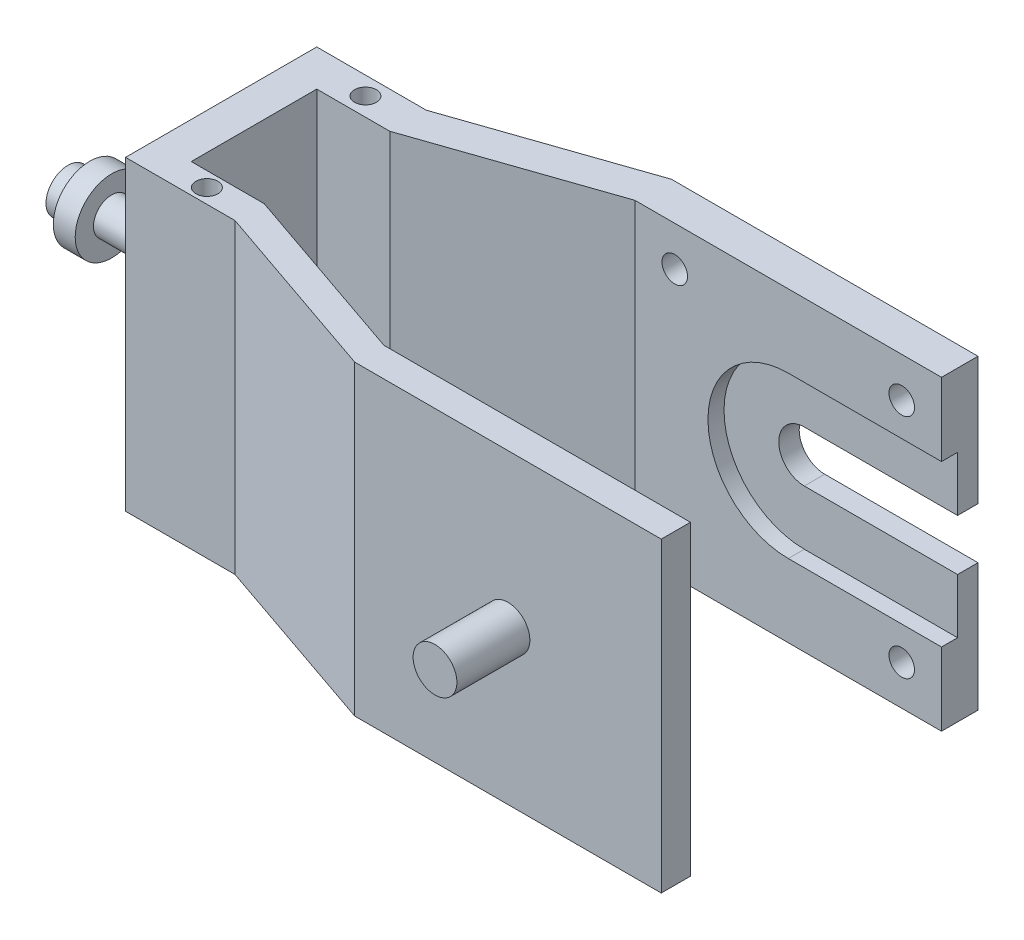
SolidWorks part; units mm, degrees
ref_plane "Front Plane" through (0, 0, 0) normal (0, 0, 1) x (1, 0, 0)
ref_plane "Top Plane" through (0, 0, 0) normal (0, 1, 0) x (1, 0, 0)
ref_plane "Right Plane" through (0, 0, 0) normal (1, 0, 0) x (0, 0, -1)
sketch "Sketch1" plane through (0, 0, 0) normal (0, 1, 0) x (1, 0, 0)
  line L0 (0, 0) -> (0, 17.2)
  line L1 (0, 0) -> (0, -17.2)
  line L2 (0, 17.2) -> (-42, 17.2)
  line L3 (0, -17.2) -> (-42, -17.2)
  line L4 (0, 0) -> (-77, 0)
  line L5 (0, 8.6) -> (-67, 8.6)
  line L6 (0, -8.6) -> (-67, -8.6)
  line L7 (-42, 17.2) -> (-67, 8.6)
  line L8 (-77, 8.6) -> (-67, 8.6)
  line L9 (-77, 8.6) -> (-77, -8.6)
  line L10 (-77, -8.6) -> (-67, -8.6)
  line L11 (-67, -8.6) -> (-42, -17.2)
  line L12 (0, 17.2) -> (0, 22.2)
  line L13 (0, 22.2) -> (-42, 22.2)
  line L14 (-67, 13.6) -> (-82, 13.6)
  line L15 (-67, 13.6) -> (-42, 22.2)
  line L16 (-82, 13.6) -> (-82, -12.6)
  line L17 (-82, -12.6) -> (-67, -12.6)
  line L18 (-42, -21.2) -> (0, -21.2)
  line L19 (-42, -21.2) -> (-67, -12.6)
  line L20 (0, -21.2) -> (0, -17.2)
  dimension "D1" = 17.2
  dimension "D2" = 17.2
  dimension "D3" = 42
  dimension "D4" = 42
  dimension "D5" = 77
  dimension "D6" = 67
  dimension "D7" = 67
  dimension "D8" = 5
  dimension "D9" = 5
  dimension "D10" = 15
  dimension "D11" = 26.2
  dimension "D12" = 4
extrude "Boss-Extrude1" add sketch "Sketch1" along normal blind 42 contours L14 L16 L17 L19 L18 L20 L3 L11 L10 L9 L8 L7 L2 L12 L13 L15
sketch "Sketch3" plane through (0, 0, -17.2) normal (0, 0, 1) x (1, 0, 0)
  line L0 (-42, 42) -> (0, 42)
  line L1 (-21, 42) -> (-21, 0)
  line L2 (0, 0) -> (-42, 0) construction
  line L3 (-21, 32) -> (0, 32)
  line L4 (0, 42) -> (0, 0) construction
  line L5 (-21, 10) -> (0, 10)
  line L6 (0, 10) -> (0, 32)
  arc A0 (-21, 32) -> (-21, 10) centre (-21, 21) ccw
  dimension "D1" = 22
extrude "Cut-Extrude2" cut sketch "Sketch3" against normal blind 2.2 contours L3 L6 L5 A0
sketch "Sketch4" plane through (0, 0, -17.2) normal (0, 0, 1) x (1, 0, 0)
  line L0 (-21, 24.5) -> (0, 24.5)
  line L1 (0, 10) -> (0, 32) construction
  line L2 (0, 24.5) -> (0, 17.5)
  line L3 (0, 17.5) -> (-21, 17.5)
  arc A0 (-21, 24.5) -> (-21, 17.5) centre (-21, 21) ccw
  dimension "D1" = 7
extrude "Cut-Extrude3" cut sketch "Sketch4" against normal up to surface (5 mm away) up to face at (-21, 21, -22.2)
sketch "Sketch7" plane through (0, 0, -22.2) normal (0, 0, -1) x (-1, 0, 0)
  line L0 (42, 42) -> (0, 42) construction
  line L1 (0, 42) -> (0, 24.5) construction
  line L2 (42, 42) -> (42, 0) construction
  line L3 (0, 0) -> (42, 0) construction
  circle A0 centre (5.45, 36.55) radius 1.75
  circle A1 centre (36.55, 36.55) radius 1.75
  circle A2 centre (5.45, 5.45) radius 1.75
  circle A3 centre (36.55, 5.45) radius 1.75
  dimension "D1" = 3.5
  dimension "D2" = 3.5
  dimension "D3" = 3.5
  dimension "D4" = 3.5
  dimension "D5" = 5.45
  dimension "D6" = 5.45
  dimension "D7" = 5.45
  dimension "D8" = 5.45
  dimension "D9" = 5.45
  dimension "D10" = 5.45
  dimension "D11" = 5.45
  dimension "D12" = 5.45
extrude "Cut-Extrude5" cut sketch "Sketch7" against normal up to surface (5 mm away) contours A3 | A2 | A1 | A0 up to face at (-17.125, 21, -17.2)
sketch "Sketch8" plane through (-82, 0, 0) normal (-1, 0, 0) x (0, 0, 1)
  line L0 (-0.5, 42) -> (-0.5, 0)
  line L1 (-13.6, 42) -> (12.6, 42) construction
  line L2 (-13.6, 0) -> (12.6, 0) construction
  circle A0 centre (-0.5, 21) radius 2.5
  dimension "D1" = 5
extrude "Boss-Extrude2" add sketch "Sketch8" along normal blind 15 contours A0
sketch "Sketch9" plane through (0, 0, 17.2) normal (0, 0, -1) x (-1, 0, 0)
  line L0 (42, 21) -> (0, 21)
  line L1 (42, 42) -> (42, 0) construction
  line L2 (0, 42) -> (0, 0) construction
  circle A0 centre (21, 21) radius 3
  dimension "D1" = 6
extrude "Boss-Extrude3" add sketch "Sketch9" against normal blind 14 contours A0
sketch "Sketch10" plane through (0, 42, 0) normal (0, 1, 0) x (1, 0, 0)
  line L0 (-82, 13.6) -> (-72.8457, 13.6)
  line L1 (-67, 13.6) -> (-82, 13.6) construction
  line L2 (-72.8457, 11.1143) -> (-72.8457, -10.6073)
  line L3 (-82, -12.6) -> (-67, -12.6) construction
  line L4 (-72.8457, -12.6) -> (-82, -12.6)
  line L5 (-72.8457, -12.6) -> (-72.8457, -8.6145)
  line L6 (-72.8457, 8.6286) -> (-72.8457, 13.6)
  circle A0 centre (-72.8457, 11.1143) radius 1.5
  circle A1 centre (-72.8457, -10.6073) radius 1.5
  dimension "D1" = 3
  dimension "D2" = 3
  dimension "D3" = 21.7216
extrude "Cut-Extrude6" cut sketch "Sketch10" against normal blind 10 contours A1 | A0
sketch "Sketch11" plane through (-97, 0, 0) normal (-1, 0, 0) x (0, 0, 1)
  circle A0 centre (-0.5, 21) radius 5
  dimension "D1" = 10
extrude "Boss-Extrude4" add sketch "Sketch11" along normal blind 3
sketch "Sketch12" plane through (-100, 0, 0) normal (-1, 0, 0) x (0, 0, 1)
  circle A0 centre (-0.5, 21) radius 3
  dimension "D1" = 6
extrude "Boss-Extrude5" add sketch "Sketch12" along normal blind 3
